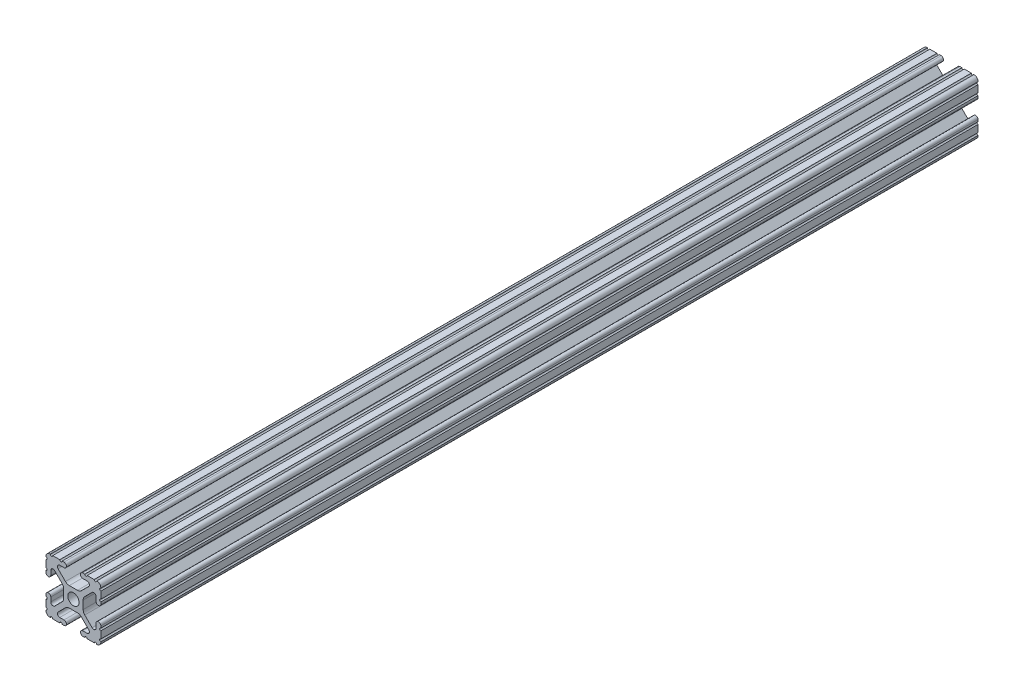
SolidWorks part; units mm, degrees
ref_plane "Front Plane" through (0, 0, 0) normal (0, 0, 1) x (1, 0, 0)
ref_plane "Top Plane" through (0, 0, 0) normal (0, 1, 0) x (1, 0, 0)
ref_plane "Right Plane" through (0, 0, 0) normal (1, 0, 0) x (0, 0, -1)
sketch "Sketch1" plane through (0, 0, 0) normal (0, 0, 1) x (1, 0, 0)
  line L0 (0, -12.7) -> (0, 12.7) construction
  line L1 (12.7, 0) -> (-12.7, 0) construction
  line L2 (3.2512, 12.7) -> (-3.2512, 12.7) construction
  line L3 (0, -4.5212) -> (0, 4.5212) construction
  line L4 (-3.2512, 12.7) -> (-3.2512, 10.4902) construction
  line L5 (12.7, -7.4168) -> (12.7, 7.4168) construction
  line L6 (0, -2.6035) -> (0, 2.6035) construction
  point P4 (0, 0)
  point P8 (0, 0)
  point P11 (0, 12.7)
  point P14 (0, 0)
  point P18 (12.7, 0)
  point P21 (0, 0)
sketch "Sketch2" plane through (0, 0, 0) normal (1, 0, 0) x (0, 0, -1)
  line L0 (-203.2, 0) -> (203.2, 0) construction
  point P4 (0, 0)
  dimension "Length" = 406.4
sketch "Sketch3" plane through (0, 0, 0) normal (0, 0, 1) x (1, 0, 0)
  line L1 (12.7, -12.7) -> (-12.7, -12.7)
  line L2 (12.7, -12.7) -> (12.7, 12.7)
  line L3 (12.7, 12.7) -> (-12.7, 12.7)
  line L4 (-12.7, -12.7) -> (-12.7, 12.7)
  line L5 (12.7, -12.7) -> (-12.7, 12.7) construction
  line L6 (12.7, 12.7) -> (-12.7, -12.7) construction
  point P0 (0, 0)
extrude "Boss-Extrude1" add sketch "Sketch3" along normal up to vertex (203.2 mm away) and the other way up to vertex (203.2 mm away) up to point (0, 0, 203.2) other way up to point (0, 0, -203.2)
sketch "Sketch4" plane through (0, 0, 203.2) normal (0, 0, 1) x (1, 0, 0)
  line L0 (-3.2512, 12.7) -> (-3.2512, 10.4902)
  line L1 (-3.2512, 10.4902) -> (-8.9276, 10.4902)
  line L2 (-8.9276, 10.4902) -> (-2.9586, 4.5212)
  line L3 (-2.9586, 4.5212) -> (2.9586, 4.5212)
  line L4 (0, -12.7) -> (0, 12.7) construction
  line L5 (12.7, 12.7) -> (-12.7, 12.7) construction
  line L6 (0, 12.7) -> (0, -12.7) construction
  line L7 (-12.7, 0) -> (12.7, 0) construction
  line L8 (-12.7, 12.7) -> (0, 0) construction
  line L9 (-12.7, 3.2512) -> (-10.4902, 3.2512)
  line L10 (-10.4902, 3.2512) -> (-10.4902, 8.9276)
  line L11 (-10.4902, 8.9276) -> (-4.5212, 2.9586)
  line L12 (-4.5212, 2.9586) -> (-4.5212, -2.9586)
  line L13 (4.5212, 2.9586) -> (4.5212, -2.9586)
  line L14 (10.4902, 8.9276) -> (4.5212, 2.9586)
  line L15 (10.4902, 3.2512) -> (10.4902, 8.9276)
  line L16 (12.7, 3.2512) -> (10.4902, 3.2512)
  line L17 (8.9276, 10.4902) -> (2.9586, 4.5212)
  line L18 (3.2512, 10.4902) -> (8.9276, 10.4902)
  line L19 (3.2512, 12.7) -> (3.2512, 10.4902)
  line L20 (3.2512, -12.7) -> (3.2512, -10.4902)
  line L21 (3.2512, -10.4902) -> (8.9276, -10.4902)
  line L22 (8.9276, -10.4902) -> (2.9586, -4.5212)
  line L23 (12.7, -3.2512) -> (10.4902, -3.2512)
  line L24 (10.4902, -3.2512) -> (10.4902, -8.9276)
  line L25 (10.4902, -8.9276) -> (4.5212, -2.9586)
  line L26 (-10.4902, -8.9276) -> (-4.5212, -2.9586)
  line L27 (-10.4902, -3.2512) -> (-10.4902, -8.9276)
  line L28 (-12.7, -3.2512) -> (-10.4902, -3.2512)
  line L29 (-2.9586, -4.5212) -> (2.9586, -4.5212)
  line L30 (-8.9276, -10.4902) -> (-2.9586, -4.5212)
  line L31 (-3.2512, -10.4902) -> (-8.9276, -10.4902)
  line L32 (-3.2512, -12.7) -> (-3.2512, -10.4902)
  line L33 (-12.7, 3.2512) -> (-12.7, -3.2512)
  line L34 (-3.2512, -12.7) -> (3.2512, -12.7)
  line L35 (12.7, -3.2512) -> (12.7, 3.2512)
  line L36 (3.2512, 12.7) -> (-3.2512, 12.7)
  line L37 (-12.7, 12.7) -> (-12.7, -12.7) construction
  line L38 (-12.7, -12.7) -> (12.7, -12.7) construction
  arc A3 (-6.3485, 10.4902) -> (-7.1039, 8.6665) centre (-6.3485, 9.4219) ccw
  arc A4 (7.1039, 8.6665) -> (6.3485, 10.4902) centre (6.3485, 9.4219) ccw
  arc A5 (8.6665, -7.1039) -> (10.4902, -6.3485) centre (9.4219, -6.3485) ccw
  arc A6 (10.4902, 6.3485) -> (8.6665, 7.1039) centre (9.4219, 6.3485) ccw
  arc A7 (-7.1039, -8.6665) -> (-6.3485, -10.4902) centre (-6.3485, -9.4219) ccw
  arc A8 (6.3485, -10.4902) -> (7.1039, -8.6665) centre (6.3485, -9.4219) ccw
  arc A9 (-8.6665, 7.1039) -> (-10.4902, 6.3485) centre (-9.4219, 6.3485) ccw
  arc A10 (-10.4902, -6.3485) -> (-8.6665, -7.1039) centre (-9.4219, -6.3485) ccw
  circle A11 centre (0, 0) radius 2.6035
  point P34 (0, 4.5212)
  point P45 (4.5212, 0)
  point P46 (-4.5212, 0)
  point P53 (0, -4.5212)
  point P81 (0, 0)
  line M2 (-12.7, 12.7) -> (-12.7, -12.7)
  line M3 (-12.7, -12.7) -> (12.7, -12.7)
  line M4 (12.7, -12.7) -> (12.7, 12.7)
  line M5 (12.7, 12.7) -> (-12.7, 12.7)
  dimension "D5" = 5.207
  dimension "D1" = 2.2098
  dimension "D2" = 2.2098
  dimension "D3" = 14.8336
  dimension "D4" = 4
extrude "Cut-Extrude1" cut sketch "Sketch4" against normal through all contours L17 A4 L18 L19 L0 L1 A3 L2 L3 M5 | L15 A6 L14 L13 L25 A5 L24 L23 L16 M4 | L21 A8 L22 L29 L30 A7 L31 L32 L20 M3 | L27 A10 L26 L12 L11 A9 L10 L9 L28 M2 | A11
sketch "Sketch5" plane through (0, 0, 203.2) normal (0, 0, 1) x (1, 0, 0)
  line L0 (-4.3561, 12.7) -> (-3.2512, 12.7)
  line L1 (-3.2512, 12.7) -> (-3.2512, 10.4902)
  line L2 (-3.2512, 10.4902) -> (-4.3561, 10.4902)
  line L3 (0, -12.7) -> (0, 12.7) construction
  line L4 (-3.2512, 12.7) -> (-12.7, 12.7) construction
  line L5 (3.2512, 10.4902) -> (4.3561, 10.4902)
  line L6 (3.2512, 12.7) -> (3.2512, 10.4902)
  line L7 (4.3561, 12.7) -> (3.2512, 12.7)
  line L8 (12.7, 4.3561) -> (12.7, 3.2512)
  line L9 (12.7, 3.2512) -> (10.4902, 3.2512)
  line L10 (10.4902, 3.2512) -> (10.4902, 4.3561)
  line L11 (10.4902, -3.2512) -> (10.4902, -4.3561)
  line L12 (12.7, -3.2512) -> (10.4902, -3.2512)
  line L13 (12.7, -4.3561) -> (12.7, -3.2512)
  line L14 (4.3561, -12.7) -> (3.2512, -12.7)
  line L15 (3.2512, -12.7) -> (3.2512, -10.4902)
  line L16 (3.2512, -10.4902) -> (4.3561, -10.4902)
  line L17 (-3.2512, -10.4902) -> (-4.3561, -10.4902)
  line L18 (-3.2512, -12.7) -> (-3.2512, -10.4902)
  line L19 (-4.3561, -12.7) -> (-3.2512, -12.7)
  line L20 (-12.7, -4.3561) -> (-12.7, -3.2512)
  line L21 (-12.7, -3.2512) -> (-10.4902, -3.2512)
  line L22 (-10.4902, -3.2512) -> (-10.4902, -4.3561)
  line L23 (-10.4902, 3.2512) -> (-10.4902, 4.3561)
  line L24 (-12.7, 3.2512) -> (-10.4902, 3.2512)
  line L25 (-12.7, 4.3561) -> (-12.7, 3.2512)
  line L26 (-12.7, 12.7) -> (-12.7, 3.2512) construction
  line L27 (-10.7124, 12.7) -> (-9.6075, 12.7)
  line L28 (-6.3436, 12.7) -> (-5.2387, 12.7)
  line L29 (-12.7, 10.7124) -> (-12.7, 9.6075)
  line L30 (-12.7, 6.3436) -> (-12.7, 5.2387)
  line L31 (6.3437, 12.7) -> (5.2388, 12.7)
  line L32 (10.7125, 12.7) -> (9.6076, 12.7)
  line L33 (12.7, 10.7125) -> (12.7, 9.6075)
  line L34 (12.7, 6.3436) -> (12.7, 5.2387)
  line L35 (12.7, -6.3437) -> (12.7, -5.2388)
  line L36 (12.7, -10.7125) -> (12.7, -9.6076)
  line L37 (10.7125, -12.7) -> (9.6076, -12.7)
  line L38 (6.3437, -12.7) -> (5.2388, -12.7)
  line L39 (-6.3436, -12.7) -> (-5.2387, -12.7)
  line L40 (-10.7124, -12.7) -> (-9.6075, -12.7)
  line L41 (-12.7, -10.7125) -> (-12.7, -9.6076)
  line L42 (-12.7, -6.3437) -> (-12.7, -5.2388)
  line L43 (12.7, 12.7) -> (3.2512, 12.7) construction
  line L44 (12.7, 3.2512) -> (12.7, 12.7) construction
  arc A0 (-4.3561, 10.4902) -> (-4.3561, 12.7) centre (-4.3561, 11.5951) ccw
  arc A1 (4.3561, 10.4902) -> (4.3561, 12.7) centre (4.3561, 11.5951) cw
  arc A2 (10.4902, 4.3561) -> (12.7, 4.3561) centre (11.5951, 4.3561) ccw
  arc A3 (10.4902, -4.3561) -> (12.7, -4.3561) centre (11.5951, -4.3561) cw
  arc A4 (4.3561, -10.4902) -> (4.3561, -12.7) centre (4.3561, -11.5951) ccw
  arc A5 (-4.3561, -10.4902) -> (-4.3561, -12.7) centre (-4.3561, -11.5951) cw
  arc A6 (-10.4902, -4.3561) -> (-12.7, -4.3561) centre (-11.5951, -4.3561) ccw
  arc A7 (-10.4902, 4.3561) -> (-12.7, 4.3561) centre (-11.5951, 4.3561) cw
  arc A8 (-10.7124, 12.7) -> (-9.6075, 12.7) centre (-10.16, 12.7) ccw
  arc A9 (-6.3436, 12.7) -> (-5.2387, 12.7) centre (-5.7912, 12.7) ccw
  arc A10 (-12.7, 9.6075) -> (-12.7, 10.7124) centre (-12.7, 10.16) ccw
  arc A11 (-12.7, 5.2387) -> (-12.7, 6.3436) centre (-12.7, 5.7912) ccw
  arc A12 (5.2388, 12.7) -> (6.3437, 12.7) centre (5.7912, 12.7) ccw
  arc A13 (9.6076, 12.7) -> (10.7125, 12.7) centre (10.16, 12.7) ccw
  arc A14 (12.7, 10.7125) -> (12.7, 9.6075) centre (12.7, 10.16) ccw
  arc A15 (12.7, 6.3436) -> (12.7, 5.2387) centre (12.7, 5.7912) ccw
  arc A16 (12.7, -5.2388) -> (12.7, -6.3437) centre (12.7, -5.7912) ccw
  arc A17 (12.7, -9.6076) -> (12.7, -10.7125) centre (12.7, -10.16) ccw
  arc A18 (10.7125, -12.7) -> (9.6076, -12.7) centre (10.16, -12.7) ccw
  arc A19 (6.3437, -12.7) -> (5.2388, -12.7) centre (5.7912, -12.7) ccw
  arc A20 (-5.2387, -12.7) -> (-6.3436, -12.7) centre (-5.7912, -12.7) ccw
  arc A21 (-9.6075, -12.7) -> (-10.7124, -12.7) centre (-10.16, -12.7) ccw
  arc A22 (-12.7, -10.7125) -> (-12.7, -9.6076) centre (-12.7, -10.16) ccw
  arc A23 (-12.7, -6.3437) -> (-12.7, -5.2388) centre (-12.7, -5.7912) ccw
  point P11 (0, 0)
  point P52 (0, 0)
  point P104 (0, 0)
  line M5 (3.2512, -10.4902) -> (3.2512, -12.7)
  line M6 (3.2512, -12.7) -> (12.7, -12.7)
  line M7 (12.7, -12.7) -> (12.7, -3.2512)
  line M8 (12.7, -3.2512) -> (10.4902, -3.2512)
  line M9 (10.4902, -3.2512) -> (10.4902, -6.3485)
  line M15 (10.4902, 6.3485) -> (10.4902, 3.2512)
  line M16 (10.4902, 3.2512) -> (12.7, 3.2512)
  line M17 (12.7, 3.2512) -> (12.7, 12.7)
  line M18 (12.7, 12.7) -> (3.2512, 12.7)
  line M19 (3.2512, 12.7) -> (3.2512, 10.4902)
  line M20 (3.2512, 10.4902) -> (6.3485, 10.4902)
  line M26 (-6.3485, 10.4902) -> (-3.2512, 10.4902)
  line M27 (-3.2512, 10.4902) -> (-3.2512, 12.7)
  line M28 (-3.2512, 12.7) -> (-12.7, 12.7)
  line M29 (-12.7, 12.7) -> (-12.7, 3.2512)
  line M30 (-12.7, 3.2512) -> (-10.4902, 3.2512)
  line M31 (-10.4902, 3.2512) -> (-10.4902, 6.3485)
  line M37 (-10.4902, -6.3485) -> (-10.4902, -3.2512)
  line M38 (-10.4902, -3.2512) -> (-12.7, -3.2512)
  line M39 (-12.7, -3.2512) -> (-12.7, -12.7)
  line M40 (-12.7, -12.7) -> (-3.2512, -12.7)
  line M41 (-3.2512, -12.7) -> (-3.2512, -10.4902)
  line M42 (-3.2512, -10.4902) -> (-6.3485, -10.4902)
  line M48 (6.3485, -10.4902) -> (3.2512, -10.4902)
  dimension "D2" = 0.5524
  dimension "D3" = 2.54
  dimension "D4" = 2.54
  dimension "D5" = 2.54
  dimension "D6" = 2.54
  dimension "D1" = 4
  dimension "D7" = 4
extrude "Cut-Extrude2" cut sketch "Sketch5" against normal through all contours A7 M30 M29 | A7 L24 M31 | A6 L21 M39 | A6 M37 M38 | A5 L18 M42 | A5 M41 M40 | A4 M48 M5 | A4 L15 M6 | A3 L12 M9 | A3 M8 M7 | A2 M15 M16 | A2 L9 M17 | A1 M19 M18 | A1 L6 M20 | A0 L1 M28 | A0 M26 M27 | A11 L30 | A10 L29 | A8 L27 | A9 L28 | L31 A12 | L32 A13 | L33 A14 | L34 A15 | L42 A23 | L41 A22 | L40 A21 | L39 A20 | L36 A17 | L35 A16 | L37 A18 | L38 A19
fillet "Fillet1" radius 2.54 8 edges at (2.9586, -4.5212, 0) (-2.9586, -4.5212, 0) (4.5212, -2.9586, 0) (4.5212, 2.9586, 0) (-2.9586, 4.5212, 0) (2.9586, 4.5212, 0) (-4.5212, -2.9586, 0) (-4.5212, 2.9586, 0)
fillet "Fillet2" radius 1.778 4 edges at (12.7, -12.7, 0) (12.7, 12.7, 0) (-12.7, -12.7, 0) (-12.7, 12.7, 0)
equation "\"D2@Sketch4\"=\"Thickness@Sketch1\""
equation "\"D1@Sketch4\"=\"Thickness@Sketch1\""
equation "\"D3@Sketch4\"=\"Opening Width@Sketch1\""
equation "\"D5@Sketch4\"=\"Hole Dia@Sketch1\""
equation "\"D2@Sketch5\"=\"Thickness@Sketch1\"/4"
equation "\"D3@Sketch5\"=\"Height@Sketch1\"/10"
equation "\"D4@Sketch5\"=\"D3@Sketch5\""
equation "\"D5@Sketch5\"=\"D4@Sketch5\""
equation "\"D6@Sketch5\"=\"D5@Sketch5\""
